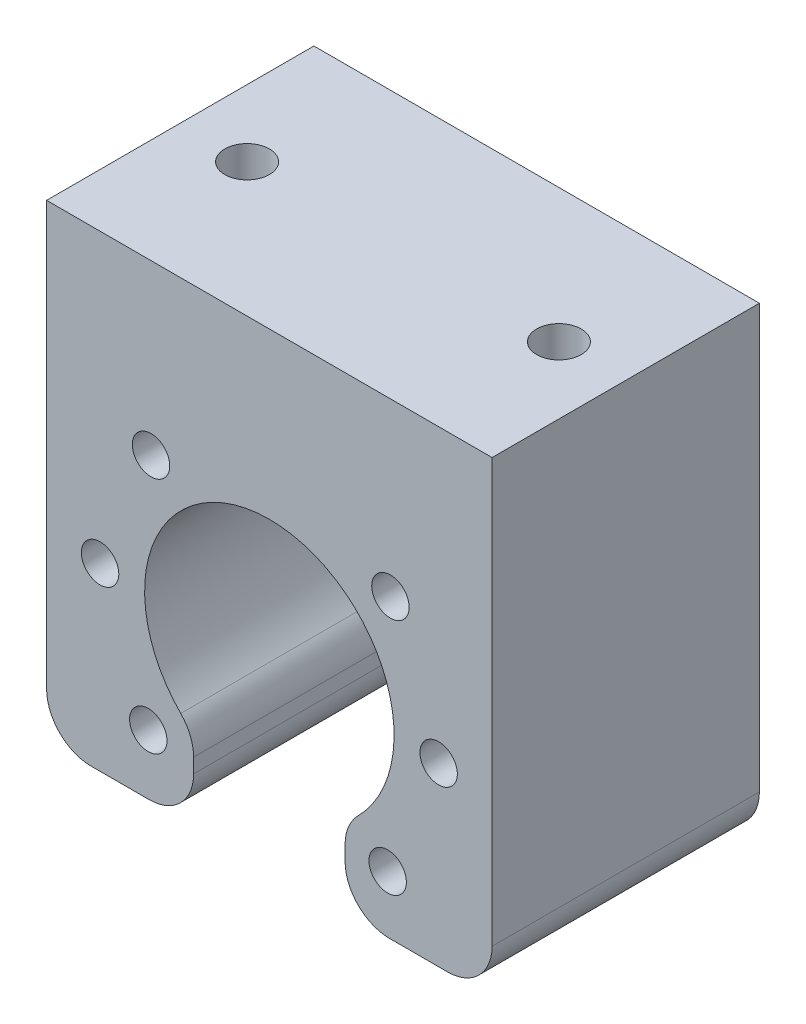
SolidWorks part; units mm, degrees
material "1023 Листовая углеродистая сталь (SS)"
ref_plane "Front" through (0, 0, 0) normal (0, 0, 1) x (1, 0, 0)
ref_plane "Top" through (0, 0, 0) normal (0, 1, 0) x (1, 0, 0)
ref_plane "Right" through (0, 0, 0) normal (1, 0, 0) x (0, 0, -1)
sketch "Sketch1" plane through (0, 0, 0) normal (0, 0, 1) x (1, 0, 0)
  line L0 (0, 0) -> (0, 32.5) construction
  line L1 (-25, 32.5) -> (25, 32.5)
  line L2 (-25, 32.5) -> (-25, -20)
  line L3 (-25, -20) -> (-8.5, -20)
  line L4 (25, 32.5) -> (25, -20)
  line L5 (8.5, -20) -> (25, -20)
  line L7 (-8.5, -11.1243) -> (-8.5, -20)
  line L9 (8.5, -11.1243) -> (8.5, -20)
  arc A0 (8.5, -11.1243) -> (-8.5, -11.1243) centre (0, 0) ccw
  dimension "D1" = 28
  dimension "D4" = 6
  dimension "D2" = 50
  dimension "D3" = 32.5
  dimension "D7" = 8.5
extrude "Extrude1" add sketch "Sketch1" along normal blind 30
fillet "Fillet1" radius 5 6 edges at (-8.5, -20, 15) (8.5, -20, 15) (8.5, -11.1243, 15) (-8.5, -11.1243, 15) (-25, -20, 15) (25, -20, 15)
hole_wizard "M5 Tapped Hole1" positions "Sketch2" profile "Sketch3" tap size "M5" standard "DIN" end condition through all
sketch "Sketch2" plane through (0, 0, 0) normal (0, 0, -1) x (-1, 0, 0)
  point P0 (-13.5885, 13.2798)
  point P3 (13.2798, 13.5885)
  point P6 (18.9987, 0.2183)
  point P9 (13.5885, -13.2798)
  point P12 (-13.2798, -13.5885)
  point P15 (-18.9987, -0.2183)
sketch "Sketch3" plane through (13.5885, 13.2798, 0) normal (1, 0, 0) x (0, 1, 0)
  line L0 (0, 0) -> (0, 30)
  line L1 (0, 30) -> (2.1, 30)
  line L2 (2.1, 30) -> (2.1, 0)
  line L5 (2.1, 0) -> (0, 0)
  line L11 (0, -6.35) -> (0, 107.95) construction
  dimension "Диаметр проходного сверла" = 4.2
  dimension "Глубина проходного сверла" = 30
cosmetic thread "Cosmetic Thread1" parameters "D2"=5
cosmetic thread "Cosmetic Thread2" parameters "D2"=5
cosmetic thread "Cosmetic Thread3" parameters "D2"=5
cosmetic thread "Cosmetic Thread4" parameters "D2"=5
cosmetic thread "Cosmetic Thread5" parameters "D2"=5
cosmetic thread "Cosmetic Thread6" parameters "D2"=5
hole_wizard "M6 Tapped Hole1" positions "Sketch4" profile "Sketch6" tap size "M6" standard "DIN"
sketch "Sketch4" plane through (0, 32.5, 0) normal (0, 1, 0) x (1, 0, 0)
  point P0 (-17.5, -15)
  point P3 (17.5, -15)
sketch "Sketch6" plane through (-17.5, 32.5, 15) normal (1, 0, 0) x (0, 0, 1)
  line L0 (0, 0) -> (0, 21.5022)
  line L1 (0, 21.5022) -> (2.5, 20)
  line L2 (2.5, 20) -> (2.5, 0)
  line L5 (2.5, 0) -> (0, 0)
  line L10 (0, 21.5022) -> (-2.5, 20) construction
  line L11 (0, -6.35) -> (0, 107.95) construction
  dimension "Диаметр сверла" = 5
  dimension "Глубина сверла" = 20
  dimension "Угол заточки сверла" = 118
cosmetic thread "Cosmetic Thread7" parameters "D1"=12, "D2"=6
cosmetic thread "Cosmetic Thread8" parameters "D1"=12, "D2"=6
